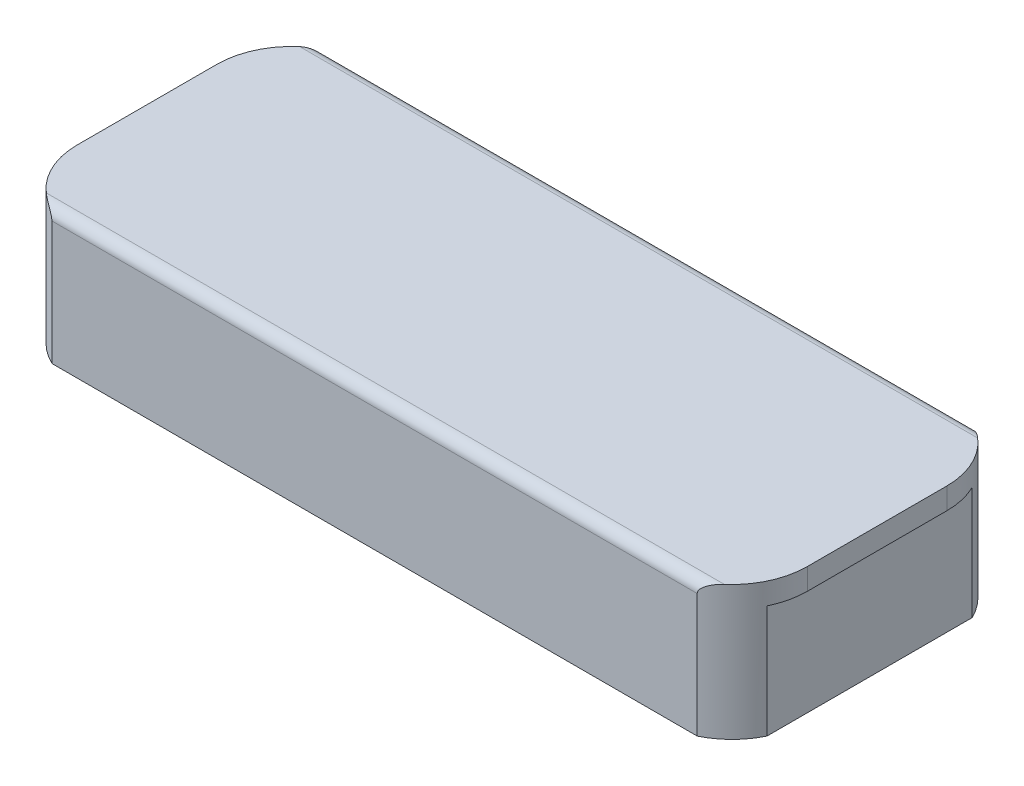
SolidWorks part; units mm, degrees
material "6061-T6 (SS)"
ref_plane "Front Plane" through (0, 0, 0) normal (0, 0, 1) x (1, 0, 0)
ref_plane "Top Plane" through (0, 0, 0) normal (0, 1, 0) x (1, 0, 0)
ref_plane "Right Plane" through (0, 0, 0) normal (1, 0, 0) x (0, 0, -1)
sketch "Sketch1" plane through (0, 0, 0) normal (0, 1, 0) x (1, 0, 0)
  line L1 (-215.9, -85.725) -> (215.9, -85.725)
  line L2 (-215.9, -85.725) -> (-215.9, 85.725)
  line L3 (-215.9, 85.725) -> (215.9, 85.725)
  line L4 (215.9, -85.725) -> (215.9, 85.725)
  line L5 (-215.9, -85.725) -> (215.9, 85.725) construction
  line L6 (-215.9, 85.725) -> (215.9, -85.725) construction
  point P0 (0, 0)
  dimension "D1" = 431.8
  dimension "D2" = 171.45
extrude "Boss-Extrude1" add sketch "Sketch1" along normal blind 85.725
sketch "Sketch2" plane through (0, 0, 0) normal (0, -1, 0) x (1, 0, 0)
  line L0 (-162.1689, -76.6864) -> (-162.1689, -85.725) construction
  line L1 (215.9, -85.725) -> (-215.9, -85.725) construction
  line L2 (-206.8614, -31.9939) -> (-215.9, -31.9939) construction
  line L3 (-215.9, -85.725) -> (-215.9, 85.725) construction
  line L4 (162.1689, -76.6864) -> (162.1689, -85.725) construction
  line L5 (206.8614, -31.9939) -> (215.9, -31.9939) construction
  line L6 (215.9, 85.725) -> (215.9, -85.725) construction
  line L7 (-162.1689, 76.6864) -> (-162.1689, 85.725) construction
  line L8 (-215.9, 85.725) -> (215.9, 85.725) construction
  line L9 (-206.8614, 31.9939) -> (-215.9, 31.9939) construction
  line L10 (206.8614, 31.9939) -> (215.9, 31.9939) construction
  line L11 (162.1689, 76.6864) -> (162.1689, 85.725)
  line L18 (162.1689, 76.6864) -> (-162.1689, 76.6864)
  line L19 (206.8614, -31.9939) -> (206.8614, 31.9939)
  line L20 (-162.1689, -76.6864) -> (162.1689, -76.6864)
  line L21 (-206.8614, 31.9939) -> (-206.8614, -31.9939)
  arc A0 (206.8614, -31.9939) -> (162.1689, -76.6864) centre (162.1689, -31.9939) cw
  arc A1 (162.1689, 76.6864) -> (206.8614, 31.9939) centre (162.1689, 31.9939) cw
  arc A2 (-162.1689, 76.6864) -> (-206.8614, 31.9939) centre (-162.1689, 31.9939) ccw
  arc A3 (-162.1689, -76.6864) -> (-206.8614, -31.9939) centre (-162.1689, -31.9939) cw
  dimension "D2" = 44.6926
extrude "Cut-Extrude1" cut sketch "Sketch2" against normal offset from surface (73.025 mm away) 12.7 contours A1 L19 A0 L20 A3 L21 A2 L18 up to face at (0, 85.725, 0)
fillet "Fillet3" radius 44.45 4 edges at (215.9, 42.8625, -85.725) (215.9, 42.8625, 85.725) (-215.9, 42.8625, 85.725) (-215.9, 42.8625, -85.725)
shell "Shell1" [suppressed] thickness 9.398
sketch "Sketch3" plane through (0, 85.725, 0) normal (0, 1, 0) x (1, 0, 0)
  line L0 (215.9, -41.275) -> (215.9, 41.275) construction
  line L1 (-171.45, -85.725) -> (171.45, -85.725) construction
  line L2 (-215.9, 41.275) -> (-215.9, -41.275) construction
  line L3 (171.45, 85.725) -> (-171.45, 85.725) construction
  line L4 (215.9, -41.275) -> (215.9, 41.275)
  line L5 (-171.45, -85.725) -> (171.45, -85.725)
  line L6 (-215.9, 41.275) -> (-215.9, -41.275)
  line L7 (171.45, 85.725) -> (-171.45, 85.725)
  arc A0 (215.9, 41.275) -> (171.45, 85.725) centre (171.45, 41.275) ccw construction
  arc A1 (171.45, -85.725) -> (215.9, -41.275) centre (171.45, -41.275) ccw construction
  arc A2 (-215.9, -41.275) -> (-171.45, -85.725) centre (-171.45, -41.275) ccw construction
  arc A3 (-171.45, 85.725) -> (-215.9, 41.275) centre (-171.45, 41.275) ccw construction
  arc A4 (215.9, 41.275) -> (171.45, 85.725) centre (171.45, 41.275) ccw
  arc A5 (171.45, -85.725) -> (215.9, -41.275) centre (171.45, -41.275) ccw
  arc A6 (-215.9, -41.275) -> (-171.45, -85.725) centre (-171.45, -41.275) ccw
  arc A7 (-171.45, 85.725) -> (-215.9, 41.275) centre (-171.45, 41.275) ccw
extrude "0.25 off top" cut sketch "Sketch3" against normal blind 6.35
sketch "Sketch4" plane through (0, 0, 85.725) normal (0, 0, 1) x (1, 0, 0)
  line L1 (-215.9, 79.375) -> (215.9, 79.375)
  line L2 (-215.9, 79.375) -> (-215.9, 0)
  line L3 (-215.9, 0) -> (215.9, 0)
  line L4 (215.9, 79.375) -> (215.9, 0)
extrude "0.125" cut sketch "Sketch4" against normal blind 4.445
sketch "Sketch5" plane through (-215.9, 0, 0) normal (-1, 0, 0) x (0, 0, 1)
  line L0 (-41.275, 79.375) -> (41.275, 79.375) construction
  line L1 (-85.725, 66.675) -> (81.28, 66.675)
  line L2 (-85.725, 66.675) -> (-85.725, 0)
  line L3 (-85.725, 0) -> (81.28, 0)
  line L4 (81.28, 66.675) -> (81.28, 0)
  dimension "D1" = 12.7
extrude "1/8 in" cut sketch "Sketch5" against normal blind 4.445
sketch "Sketch6" plane through (0, 0, -85.725) normal (0, 0, -1) x (-1, 0, 0)
  line L1 (-215.9, 79.375) -> (211.455, 79.375)
  line L2 (-215.9, 79.375) -> (-215.9, 0)
  line L3 (-215.9, 0) -> (211.455, 0)
  line L4 (211.455, 79.375) -> (211.455, 0)
extrude "Cut-Extrude5" cut sketch "Sketch6" against normal blind 4.445
sketch "Sketch7" plane through (215.9, 0, 0) normal (1, 0, 0) x (0, 0, -1)
  line L0 (-41.275, 79.375) -> (-81.28, 79.375) construction
  line L1 (-80.7212, 66.675) -> (81.28, 66.675)
  line L2 (-80.7212, 66.675) -> (-80.7212, 0)
  line L3 (-80.7212, 0) -> (81.28, 0)
  line L4 (81.28, 66.675) -> (81.28, 0)
  dimension "D1" = 12.7
extrude "Cut-Extrude6" cut sketch "Sketch7" against normal blind 4.445
sketch "Sketch8" plane through (0, 0, -81.28) normal (0, 0, -1) x (-1, 0, 0)
  line L0 (-255.5825, 22.225) -> (258.7675, 22.225)
  line L1 (-190.8253, 0) -> (190.8253, 0) construction
  dimension "D1" = 22.225
split line "Split Line1"
fillet "Fillet5" radius 6.35 2 edges at (0, 79.375, -81.28) (0, 79.375, 81.28)
fillet "Fillet4" [suppressed] radius 0.762
equation "\"oring.277.ID\"= 11.484in"
equation "\"oring.277.A\"= 11.750in"
equation "\"oring.277.A1\"= 11.722in"
equation "\"oring.277.B\"= 11.500in"
equation "\"oring.277.B1\"= 11.528in"
equation "\"oring.277.C\"= 11.747in"
equation "\"oring.277.D\"= 11.503in"
equation "\"oring.277.G\"= 0.187in"
equation "\"D1@Sketch2\" = ( \"oring.279.A\" + \"anodize.add\" * 2 ) * PI"
equation "\"D2@Sketch2\"=12 * \"oring.279.W\" + ( \"oring.279.C.factor\" - \"oring.279.B1\" ) / 2"
equation "\"oring.277.W\"= 0.139in"
equation "\"anodize.add\"= 0.001in"
equation "\"c.factor\"= 0.00271"
equation "\"oring.277.C.factor\"= \"oring.277.C\" - \"oring.277.C\" * \"c.factor\""
equation "\"oring.279.ID\"= 12.984in"
equation "\"oring.279.A\"= 13.250in"
equation "\"oring.279.A1\"= 13.222in"
equation "\"oring.279.B\"= 13.000in"
equation "\"oring.279.B1\"= 13.028in"
equation "\"oring.279.C\"= 13.247in"
equation "\"oring.279.D\"= 13.003in"
equation "\"oring.279.G\"= 0.187in"
equation "\"oring.279.W\"= 0.139in"
equation "\"oring.279.C.factor\"= \"oring.279.C\" - \"oring.279.C\" * \"c.factor\""
